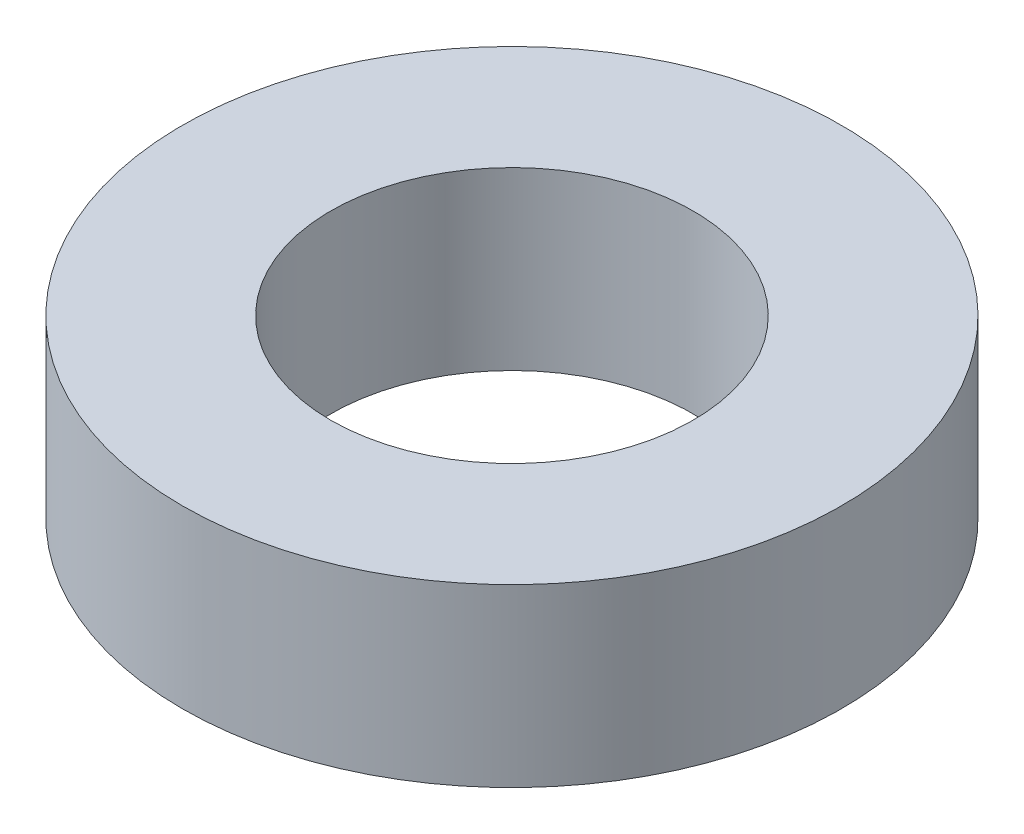
SolidWorks part; units mm, degrees
ref_plane "Front Plane" through (0, 0, 0) normal (0, 0, 1) x (1, 0, 0)
ref_plane "Top Plane" through (0, 0, 0) normal (0, 1, 0) x (1, 0, 0)
ref_plane "Right Plane" through (0, 0, 0) normal (1, 0, 0) x (0, 0, -1)
sketch "Sketch1" plane through (0, 0, 0) normal (0, 1, 0) x (1, 0, 0)
  circle A0 centre (0, 0) radius 1.65
  circle A1 centre (0, 0) radius 3
  dimension "D1" = 3.3
  dimension "D2" = 6
extrude "Boss-Extrude1" add sketch "Sketch1" along normal blind 1.6
